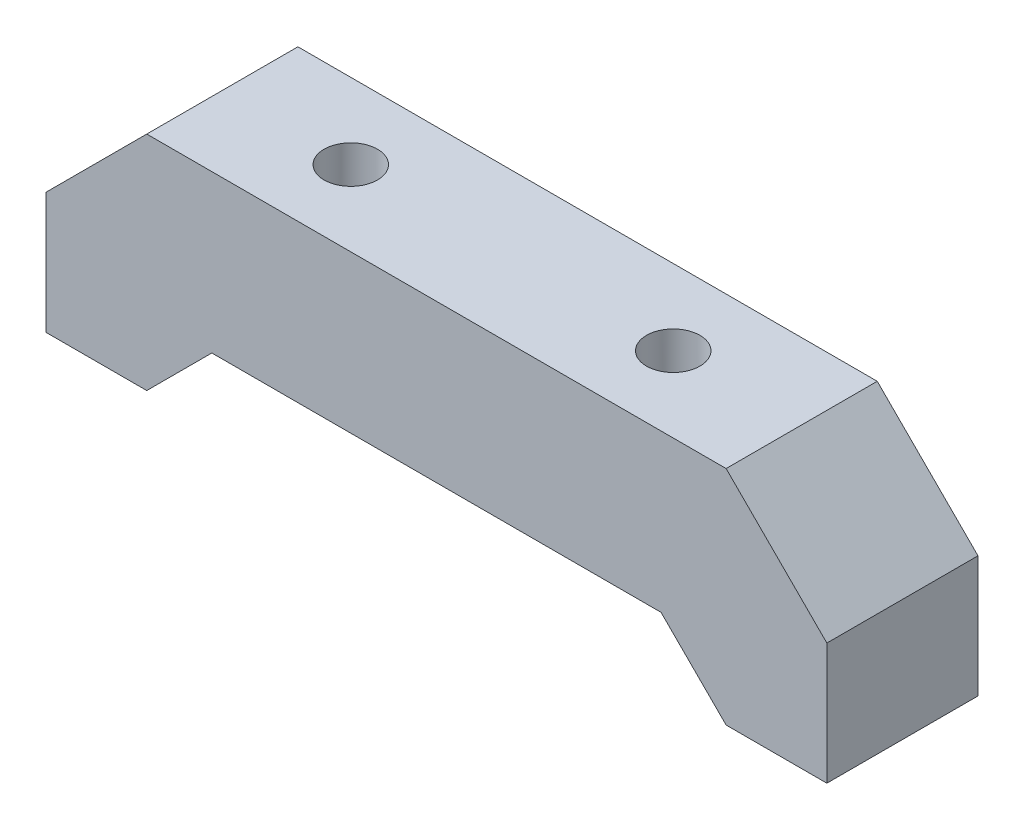
SolidWorks part; units mm, degrees
ref_plane "Front Plane" through (0, 0, 0) normal (0, 0, 1) x (1, 0, 0)
ref_plane "Top Plane" through (0, 0, 0) normal (0, 1, 0) x (1, 0, 0)
ref_plane "Right Plane" through (0, 0, 0) normal (1, 0, 0) x (0, 0, -1)
sketch "Sketch1" plane through (0, 0, 0) normal (0, 0, 1) x (1, 0, 0)
  line L0 (10.103, 8.7693) -> (67.603, 8.7693)
  line L1 (10.103, 8.7693) -> (0.103, -1.2307)
  line L2 (67.603, 8.7693) -> (77.603, -1.2307)
  line L3 (77.603, -13.279) -> (77.603, -1.2307)
  line L4 (0.103, -1.2307) -> (0.103, -13.279)
  line L5 (0.103, -13.279) -> (10.103, -13.279)
  line L6 (16.5608, -6.8212) -> (10.103, -13.279)
  line L7 (61.1453, -6.8212) -> (67.603, -13.279)
  line L8 (67.603, -13.279) -> (77.603, -13.279)
  line L9 (16.5608, -6.8212) -> (61.1453, -6.8212)
  line L10 (20.353, 8.7693) -> (20.353, -1.8212)
  line L11 (25.353, 8.7693) -> (25.353, -1.8212)
  line L12 (18.353, -1.8212) -> (27.353, -1.8212)
  line L13 (27.353, -1.8212) -> (27.353, -6.8212)
  line L14 (18.353, -1.8212) -> (18.353, -6.8212)
  line L15 (59.353, -1.8212) -> (50.353, -1.8212)
  line L16 (59.353, -1.8212) -> (59.353, -6.8212)
  line L17 (50.353, -1.8212) -> (50.353, -6.8212)
  line L18 (52.353, 8.7693) -> (52.353, -1.8212)
  line L19 (57.353, 8.7693) -> (57.353, -1.8212)
extrude "Boss-Extrude1" add sketch "Sketch1" along normal blind 15 contours L14 L12 L10 L0 L1 L4 L5 L6 L9 | L12 L14 L9 L13 | L10 L12 L11 L0 | L18 L0 L11 L12 L13 L9 L17 L15 | L15 L17 L9 L16 | L19 L0 L18 L15 | L0 L19 L15 L16 L9 L7 L8 L3 L2
sketch "Sketch2" plane through (0, 8.7693, 0) normal (0, 1, 0) x (1, 0, 0)
  line L0 (10.103, -7.5) -> (67.603, -7.5) construction
  line L1 (10.103, -15) -> (10.103, 0) construction
  line L2 (67.603, -15) -> (67.603, 0) construction
  line L3 (10.103, -15) -> (67.603, -15) construction
  line L4 (38.853, 0) -> (38.853, -15) construction
  line L5 (10.103, 0) -> (67.603, 0) construction
  circle A0 centre (22.853, -7.5) radius 2.65
  circle A1 centre (54.853, -7.5) radius 2.65
  point P8 (38.853, -15)
  dimension "D2" = 5.3
  dimension "D1" = 16
extrude "Cut-Extrude1" cut sketch "Sketch2" against normal through all
sketch "Sketch3" plane through (0, -6.8212, 0) normal (0, -1, 0) x (1, 0, 0)
  line L0 (38.853, 15) -> (38.853, 0) construction
  line L1 (16.5608, 15) -> (61.1453, 15) construction
  line L2 (16.5608, 0) -> (61.1453, 0) construction
  circle A0 centre (22.853, 7.5) radius 4.5
  circle A1 centre (54.853, 7.5) radius 4.5
  dimension "D1" = 9
extrude "Cut-Extrude2" cut sketch "Sketch3" against normal blind 5
